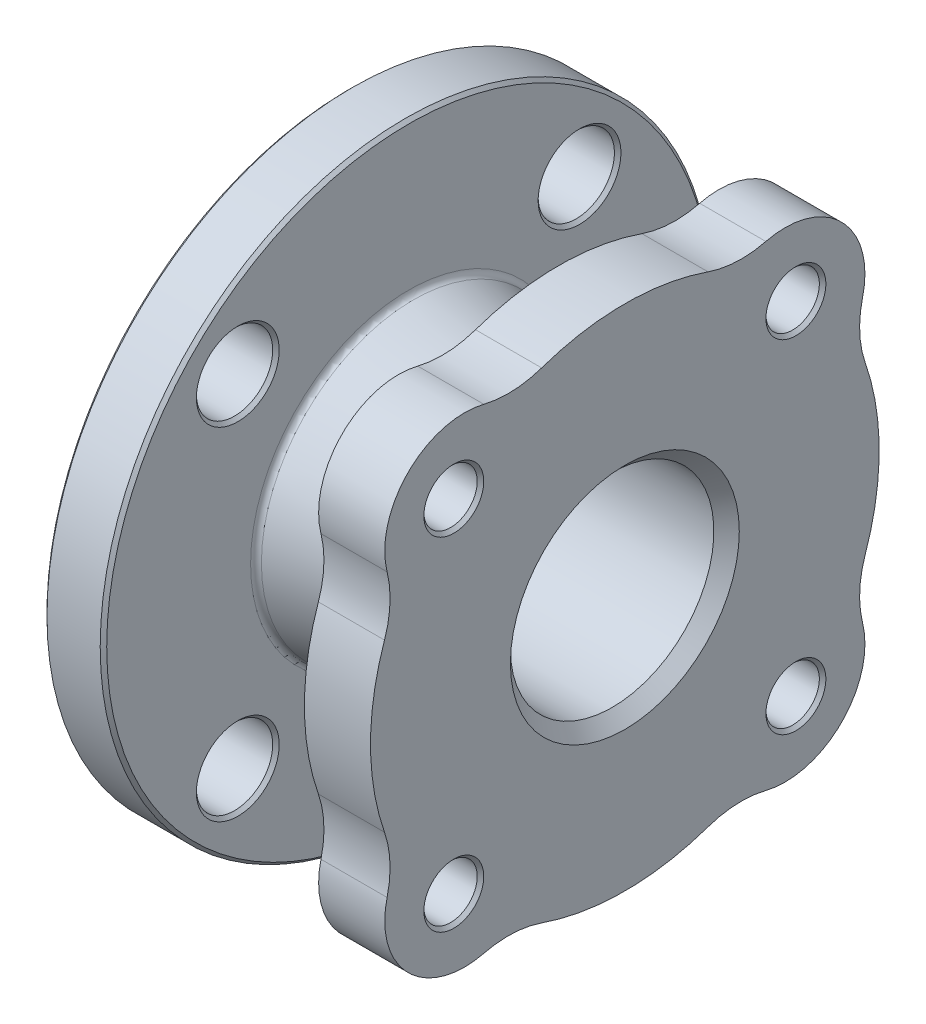
SolidWorks part; units mm, degrees
ref_plane "Front Plane" through (0, 0, 0) normal (0, 0, 1) x (1, 0, 0)
ref_plane "Top Plane" through (0, 0, 0) normal (0, 1, 0) x (1, 0, 0)
ref_plane "Right Plane" through (0, 0, 0) normal (1, 0, 0) x (0, 0, -1)
sketch "Sketch1" plane through (0, 0, 0) normal (0, 0, 1) x (1, 0, 0)
  line L0 (0, 0) -> (40.0681, 0) construction
  line L1 (0, 0) -> (0, 46.101) construction
  line L2 (0, 25.4) -> (53.975, 25.4)
  line L3 (53.975, 25.4) -> (53.975, 47.625)
  line L4 (53.975, 47.625) -> (52.3748, 46.0248)
  line L5 (52.3748, 46.0248) -> (52.3748, 34.29)
  line L6 (52.3748, 34.29) -> (35.052, 34.29)
  line L7 (35.052, 34.29) -> (16.51, 38.2312)
  line L8 (16.51, 38.2312) -> (16.51, 76.2)
  line L9 (16.51, 76.2) -> (1.6002, 76.2)
  line L10 (1.6002, 76.2) -> (1.6002, 47.7012)
  line L11 (1.6002, 47.7012) -> (0, 46.101)
  line L12 (0, 46.101) -> (0, 25.4)
  dimension "D1" = 53.975
  dimension "D2" = 50.8
  dimension "D3" = 95.25
  dimension "D4" = 1.6002
  dimension "D5" = 45
  dimension "D6" = 68.58
  dimension "D7" = 12
  dimension "D8" = 35.052
  dimension "D9" = 16.51
  dimension "D10" = 1.6002
  dimension "D11" = 45
  dimension "D12" = 152.4
  dimension "D13" = 92.202
revolve "Revolve1" add sketch "Sketch1" angle 360 about L0
sketch "Sketch2" plane through (53.975, 0, 0) normal (1, 0, 0) x (0, 0, -1)
  line L0 (-63.5, 0) -> (63.5, 0) construction
  line L1 (0, -63.5) -> (0, 63.5) construction
  line L3 (0, 0) -> (-44.9013, 44.9013) construction
  circle A0 centre (0, 0) radius 60.325 construction
  arc A1 (-60.0061, 20.7729) -> (-60.0061, -20.7729) centre (0, 0) ccw
  arc A2 (-35.2014, 59.3567) -> (-59.3567, 35.2014) centre (-40.005, 40.005) ccw
  arc A3 (35.2014, 59.3567) -> (59.3567, 35.2014) centre (40.005, 40.005) cw
  arc A4 (35.2014, -59.3567) -> (59.3567, -35.2014) centre (40.005, -40.005) ccw
  arc A5 (-20.7729, -60.0061) -> (20.7729, -60.0061) centre (0, 0) ccw
  arc A6 (20.7729, 60.0061) -> (-20.7729, 60.0061) centre (0, 0) ccw
  arc A7 (60.0061, -20.7729) -> (60.0061, 20.7729) centre (0, 0) ccw
  arc A8 (-35.2014, -59.3567) -> (-59.3567, -35.2014) centre (-40.005, -40.005) cw
  arc A9 (59.3567, -35.2014) -> (60.0061, -20.7729) centre (84.0086, -29.0821) cw
  arc A10 (35.2014, -59.3567) -> (20.7729, -60.0061) centre (29.0821, -84.0086) ccw
  arc A11 (-35.2014, -59.3567) -> (-20.7729, -60.0061) centre (-29.0821, -84.0086) cw
  arc A12 (-60.0061, -20.7729) -> (-59.3567, -35.2014) centre (-84.0086, -29.0821) cw
  arc A13 (59.3567, 35.2014) -> (60.0061, 20.7729) centre (84.0086, 29.0821) ccw
  arc A14 (35.2014, 59.3567) -> (20.7729, 60.0061) centre (29.0821, 84.0086) cw
  arc A15 (-20.7729, 60.0061) -> (-35.2014, 59.3567) centre (-29.0821, 84.0086) cw
  arc A16 (-59.3567, 35.2014) -> (-60.0061, 20.7729) centre (-84.0086, 29.0821) cw
  circle A17 centre (-42.7064, 42.7064) radius 6.6675
  circle A18 centre (42.7064, 42.7064) radius 6.6675
  circle A19 centre (42.7064, -42.7064) radius 6.6675
  circle A20 centre (-42.7064, -42.7064) radius 6.6675
  circle A21 centre (0, 0) radius 25.4 construction
  circle A22 centre (0, 0) radius 25.4
  point P22 (56.5523, -28.8806)
  point P27 (-28.8806, -56.5523)
  point P34 (28.8806, 56.5523)
  dimension "D1" = 120.65
  dimension "D2" = 127
  dimension "D7" = 39.878
  dimension "D3" = 25.4
  dimension "D5" = 13.335
  dimension "D4" = 45
  dimension "D8" = 40.005
extrude "Boss-Extrude2" add sketch "Sketch2" along normal blind 16.51
sketch "Sketch3" plane through (1.6002, 0, 0) normal (-1, 0, 0) x (0, 0, 1)
  line L0 (0, 0) -> (44.9013, 44.9013) construction
  line L1 (0, 0) -> (44.9013, 44.9013) construction
  line L2 (0, 81.2464) -> (0, -82.587) construction
  line L3 (-92.43, 0) -> (108.9059, 0) construction
  circle A0 centre (0, 0) radius 60.325 construction
  circle A1 centre (0, 0) radius 60.325 construction
  circle A2 centre (42.6562, 42.6562) radius 9.525
  circle A3 centre (-42.6562, 42.6562) radius 9.525
  circle A4 centre (42.6562, -42.6562) radius 9.525
  circle A5 centre (-42.6562, -42.6562) radius 9.525
  dimension "D1" = 19.05
extrude "Cut-Extrude1" cut sketch "Sketch3" against normal up to next
chamfer "Chamfer1" distance 0.8128 angle 45 18 edges at (53.975, -42.7064, -49.3739) (70.485, -42.7064, -49.3739) (53.975, -42.7064, 49.3739) (70.485, -42.7064, 49.3739) (53.975, 42.7064, -36.0389) (70.485, 42.7064, -36.0389) (53.975, 42.7064, 36.0389) (70.485, 42.7064, 36.0389) (16.51, -42.6562, 52.1812) (1.6002, -42.6562, 33.1312) (16.51, -42.6562, -33.1312) (1.6002, -42.6562, -33.1312) (16.51, 42.6562, 52.1812) (1.6002, 42.6562, 52.1812) (16.51, 42.6562, -33.1312) (1.6002, 42.6562, -52.1812) (16.51, 0, 76.2) (1.6002, 0, 76.2)
chamfer "Chamfer2" distance 3.175 angle 45 2 edges at (70.485, 0, -25.4) (0, 0, 25.4)
fillet "Fillet1" radius 1.524 2 edges at (52.3748, 0, 34.29) (16.51, 0, 38.2312)
